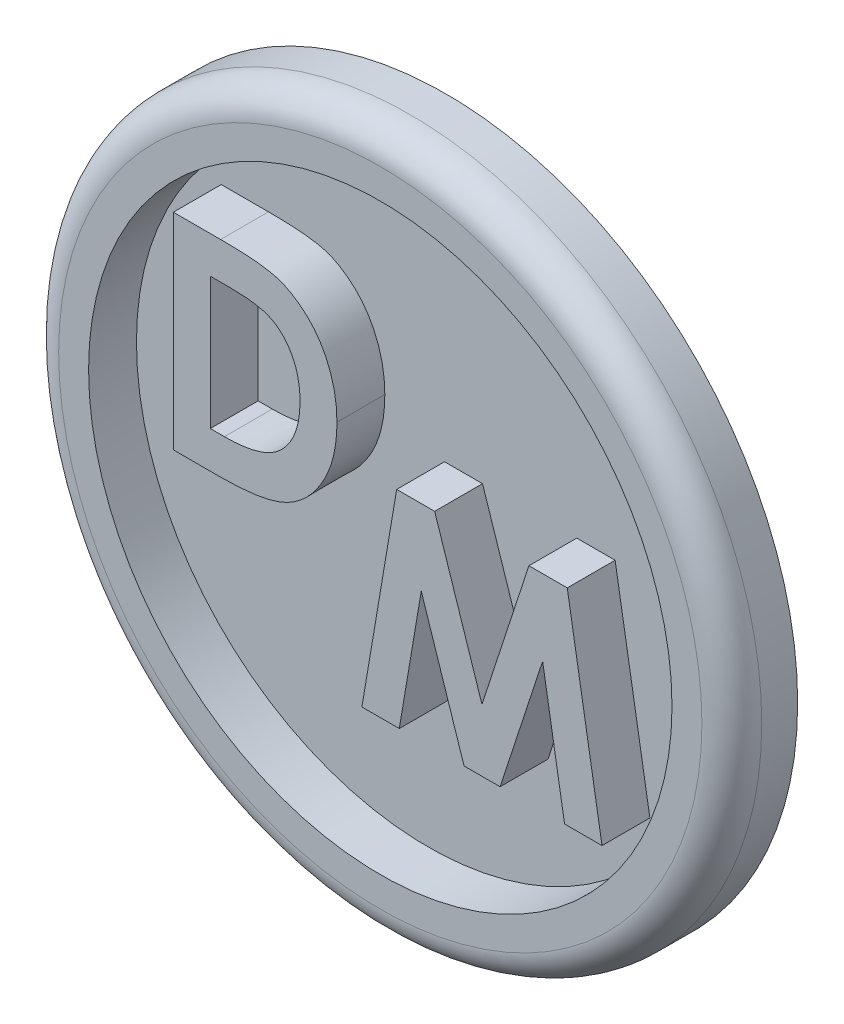
SolidWorks part; units mm, degrees
ref_plane "Front Plane" through (0, 0, 0) normal (0, 0, 1) x (1, 0, 0)
ref_plane "Top Plane" through (0, 0, 0) normal (0, 1, 0) x (1, 0, 0)
ref_plane "Right Plane" through (0, 0, 0) normal (1, 0, 0) x (0, 0, -1)
sketch "Sketch1" plane through (0, 0, 0) normal (0, 0, 1) x (1, 0, 0)
  circle A0 centre (0, 0) radius 11.75
  dimension "D1" = 23.5
extrude "Boss-Extrude1" add sketch "Sketch1" along normal blind 0.6
sketch "Sketch2" plane through (0, 0, 0.6) normal (0, 0, 1) x (1, 0, 0)
  circle A0 centre (0, 0) radius 11.75
  circle A1 centre (0, 0) radius 9.75
  dimension "D1" = 19.5
  dimension "D2" = 23.5
extrude "Boss-Extrude2" add sketch "Sketch2" along normal blind 1.6
sketch "Sketch3" plane through (0, 0, 0.6) normal (0, 0, 1) x (1, 0, 0)
  text T0 "DM" font "Century Gothic" height in points 26
extrude "Boss-Extrude3" add sketch "Sketch3" along normal blind 1.6
fillet "Fillet1" radius 1 1 edges at (11.75, 0, 2.2)
